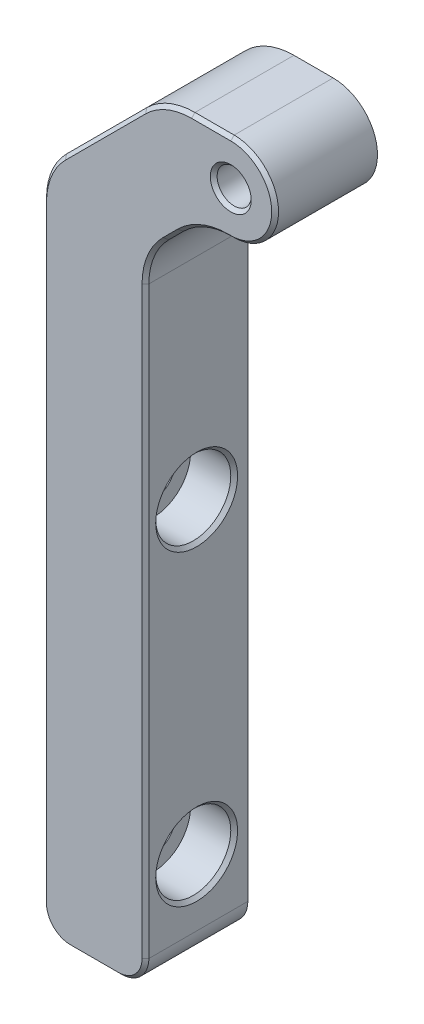
SolidWorks part; units mm, degrees
material "Alumina"
ref_plane "Plan de face" through (0, 0, 0) normal (0, 0, 1) x (1, 0, 0)
ref_plane "Plan de dessus" through (0, 0, 0) normal (0, 1, 0) x (1, 0, 0)
ref_plane "Plan de droite" through (0, 0, 0) normal (1, 0, 0) x (0, 0, -1)
sketch "Sketch1" plane through (0, 0, 0) normal (0, 0, 1) x (1, 0, 0)
  line L0 (2.9141, -75.4592) -> (9.9141, -75.4592)
  line L1 (-1.0859, -71.4592) -> (-1.0859, 17.5334)
  line L2 (13.9141, -71.4592) -> (13.9141, 14.1487)
  line L3 (26.4141, 39.2908) -> (20.6715, 39.2908)
  line L4 (13.6004, 36.3619) -> (1.843, 24.6045)
  line L5 (26.4141, 26.2908) -> (26.0562, 26.2908)
  line L6 (16.843, 21.2197) -> (18.9852, 23.3619)
  arc A1 (26.4141, 26.2908) -> (26.4141, 39.2908) centre (26.4141, 32.7908) ccw
  arc A2 (18.9852, 23.3619) -> (26.0562, 26.2908) centre (26.0562, 16.2908) cw
  arc A3 (16.843, 21.2197) -> (13.9141, 14.1487) centre (23.9141, 14.1487) ccw
  arc A4 (1.843, 24.6045) -> (-1.0859, 17.5334) centre (8.9141, 17.5334) ccw
  arc A5 (20.6715, 39.2908) -> (13.6004, 36.3619) centre (20.6715, 29.2908) ccw
  arc A6 (9.9141, -75.4592) -> (13.9141, -71.4592) centre (9.9141, -71.4592) ccw
  arc A7 (2.9141, -75.4592) -> (-1.0859, -71.4592) centre (2.9141, -71.4592) cw
  point P14 (13.9141, 26.2908)
  dimension "D1" = 6.5
  dimension "D3" = 10
  dimension "D4" = 4
  dimension "D2" = 45
extrude "Boss-Extrude1" add sketch "Sketch1" along normal blind 15
hole_wizard "Tap Drill for M6 Tap1" positions "Sketch2" profile "Sketch3" hole size "M6" standard "ISO" end condition through all
sketch "Sketch2" plane through (0, 0, 15) normal (0, 0, 1) x (1, 0, 0)
  point P0 (26.4141, 32.7908)
sketch "Sketch3" plane through (26.4141, 32.7908, 15) normal (1, 0, 0) x (0, -1, 0)
  line L0 (0, 0) -> (0, 15)
  line L1 (0, 15) -> (2.5, 15)
  line L2 (2.5, 15) -> (2.5, 0)
  line L5 (2.5, 0) -> (0, 0)
  line L11 (0, -6.35) -> (0, 107.95) construction
  dimension "Thru Hole Dia." = 5
  dimension "Thru Hole Depth" = 15
hole_wizard "CBORE for M6 Hex Socket Head Cap Screw1" positions "Sketch4" profile "Sketch5" counterbore size "M6" standard "ISO" end condition through all
sketch "Sketch4" plane through (13.9141, 0, 0) normal (1, 0, 0) x (0, 0, -1)
  line L0 (0, -71.4592) -> (0, 14.1487) construction
  line L1 (-15, 39.2908) -> (0, 39.2908) construction
  point P0 (-7.5, -16.7092)
  point P2 (-7.5, -61.7092)
  dimension "D1" = 45
  dimension "D2" = 7.5
  dimension "D3" = 56
sketch "Sketch5" plane through (13.9141, -16.7092, 7.5) normal (0, 1, 0) x (0, 0, -1)
  line L0 (0, 0) -> (0, 15)
  line L1 (0, 15) -> (3.3, 15)
  line L3 (3.3, 15) -> (3.3, 6.4)
  line L4 (3.3, 6.4) -> (5.5, 6.4)
  line L5 (5.5, 6.4) -> (5.5, 0)
  line L7 (5.5, 0) -> (0, 0)
  line L11 (0, -6.35) -> (0, 107.95) construction
  dimension "Thru Hole Dia." = 6.6
  dimension "Thru Hole Depth" = 15
  dimension "C'Bore Dia." = 11
  dimension "C'Bore Depth" = 6.4
chamfer "Chamfer1" distance 0.5 angle 45 17 edges at (13.9141, -61.7092, 2) (13.9141, -16.7092, 2) (28.9141, 32.7908, 15) (16.8446, 38.5296, 15) (7.7217, 30.4832, 15) (23.5428, 39.2908, 15) (-0.3247, 21.3603, 15) (32.9141, 32.7908, 15) (-1.0859, -26.9629, 15) (26.2352, 26.2908, 15) (0.0857, -74.2876, 15) (22.2294, 25.5296, 15) (6.4141, -75.4592, 15) (17.9141, 22.2908, 15) (12.7425, -74.2876, 15) (14.6753, 17.9755, 15) (13.9141, -28.6553, 15)
